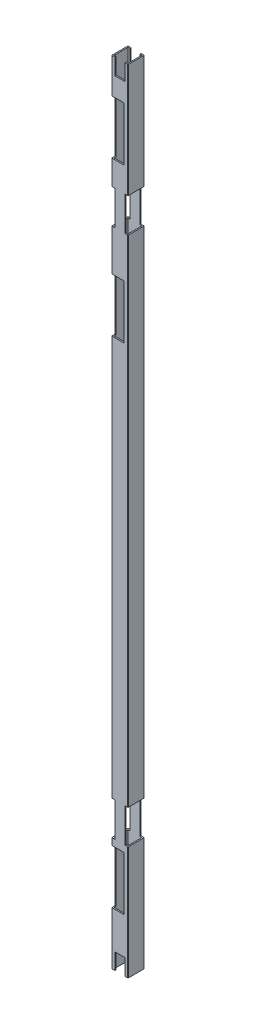
SolidWorks part; units mm, degrees
ref_plane "Front Plane" through (0, 0, 0) normal (0, 0, 1) x (1, 0, 0)
ref_plane "Top Plane" through (0, 0, 0) normal (0, 1, 0) x (1, 0, 0)
ref_plane "Right Plane" through (0, 0, 0) normal (1, 0, 0) x (0, 0, -1)
sketch "Sketch1" plane through (0, 0, 0) normal (0, 1, 0) x (1, 0, 0)
  line L0 (1.5, 1.5) -> (18.5, 1.5)
  line L1 (0.5, 0) -> (19.5, 0)
  line L2 (0, 0.5) -> (0, 19.5)
  line L3 (0.5, 20) -> (19.5, 20)
  line L4 (20, 0.5) -> (20, 19.5)
  line L5 (18.5, 1.5) -> (18.5, 18.5)
  line L6 (1.5, 18.5) -> (18.5, 18.5)
  line L7 (1.5, 1.5) -> (1.5, 18.5)
  arc A0 (19.5, 0) -> (20, 0.5) centre (19.5, 0.5) ccw
  arc A1 (0.5, 0) -> (0, 0.5) centre (0.5, 0.5) cw
  arc A2 (0, 19.5) -> (0.5, 20) centre (0.5, 19.5) cw
  arc A3 (19.5, 20) -> (20, 19.5) centre (19.5, 19.5) cw
  arc A4 (18.5, 1.5) -> (18.5, 1.5) centre (18.5, 1.5) ccw
  arc A5 (18.5, 18.5) -> (18.5, 18.5) centre (18.5, 18.5) cw
  arc A6 (1.5, 18.5) -> (1.5, 18.5) centre (1.5, 18.5) cw
  arc A7 (1.5, 1.5) -> (1.5, 1.5) centre (1.5, 1.5) cw
  point P9 (0, 0)
  dimension "D3" = 0.5
  dimension "D1" = 20
  dimension "D2" = 20
  dimension "D4" = 1.5
extrude "Boss-Extrude1" add sketch "Sketch1" along normal blind 975
sketch "Sketch2" plane through (0, 0, 0) normal (0, 0, 1) x (1, 0, 0)
  line L0 (0.5, 975) -> (19.5, 975) construction
  line L1 (16, 975) -> (4, 975)
  line L2 (16, 975) -> (16, 955)
  line L3 (16, 955) -> (4, 955)
  line L4 (4, 975) -> (4, 955)
  line L5 (20, 975) -> (20, 0) construction
  point P8 (10, 975)
  point P9 (10, 975)
  dimension "D1" = 20
  dimension "D2" = 4
extrude "Cut-Extrude1" cut sketch "Sketch2" against normal blind 1177
sketch "Sketch3" plane through (0, 0, -20) normal (0, 0, -1) x (-1, 0, 0)
  line L0 (0, 975) -> (0, 0) construction
  line L1 (0, 835) -> (-4, 835)
  line L2 (0, 835) -> (0, 792.8)
  line L3 (0, 792.8) -> (-4, 792.8)
  line L4 (-4, 835) -> (-4, 792.8)
  line L5 (-20, 975) -> (-20, 0) construction
  line L6 (-20, 835) -> (-16, 835)
  line L7 (-20, 835) -> (-20, 792.8)
  line L8 (-20, 792.8) -> (-16, 792.8)
  line L9 (-16, 835) -> (-16, 792.8)
  line L10 (-4, 975) -> (-0.5, 975) construction
  point P14 (-2, 835)
  dimension "D1" = 4
  dimension "D2" = 140
  dimension "D3" = 42.2
extrude "Cut-Extrude2" cut sketch "Sketch3" against normal blind 1177
ref_plane "Plane1" through (0, 487.5, 0) normal (0, 1, 0) x (1, 0, 0)
mirror "Mirror1" about plane through (0, 487.5, 0) normal (0, 1, 0) of "Cut-Extrude2", "Cut-Extrude1"
sketch "Sketch4" plane through (0, 0, -20) normal (0, 0, 1) x (1, 0, 0)
  line L1 (19.5, 975) -> (19.5, 835) construction
  line L3 (16, 975) -> (19.5, 975) construction
  circle A0 centre (7.75, 921.65) radius 2.1
  circle A1 centre (7.75, 875.35) radius 2.1
  dimension "D1" = 46.3
  dimension "D2" = 53.35
  dimension "D3" = 11.75
  dimension "D4" = 4.2
extrude "Cut-Extrude3" cut sketch "Sketch4" along normal blind 10
sketch "Sketch6" plane through (20, 0, 0) normal (1, 0, 0) x (0, 0, -1)
  line L0 (0, 975) -> (0, 835) construction
  line L1 (0, 931.65) -> (4, 931.65)
  line L2 (0, 931.65) -> (0, 865.35)
  line L3 (0, 865.35) -> (4, 865.35)
  line L4 (4, 931.65) -> (4, 865.35)
  line L5 (0.5, 975) -> (19.5, 975) construction
  dimension "D1" = 43.35
  dimension "D2" = 4
  dimension "D3" = 66.3
extrude "Cut-Extrude4" cut sketch "Sketch6" along normal blind 15 from offset 20 offset against normal yes
pattern_linear "LPattern1" count 2 spacing 190 along (0, -1, 0) of "Cut-Extrude3", "Cut-Extrude4"
pattern_linear "LPattern2" count 2 spacing 800 along (0, -1, 0) of "Cut-Extrude3", "Cut-Extrude4"
